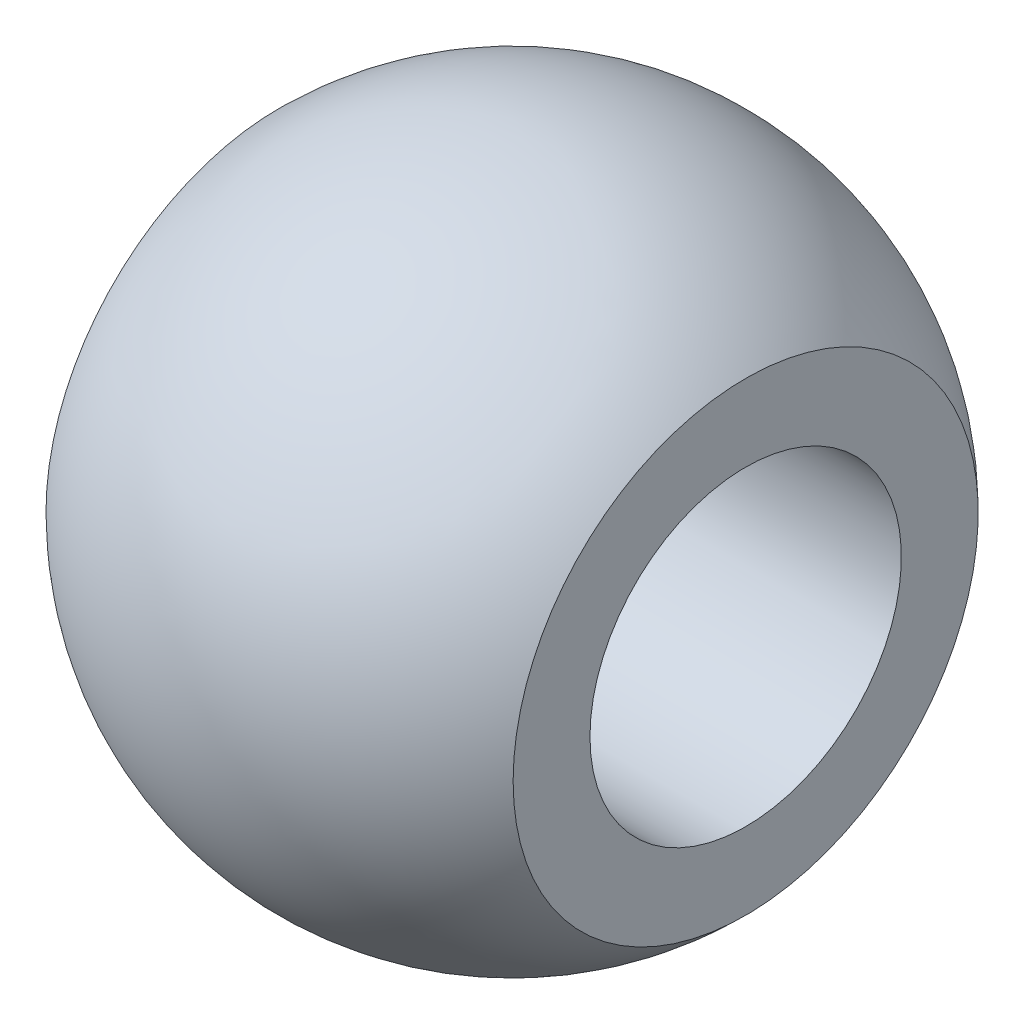
SolidWorks part; units mm, degrees
material "AISI 304"
ref_plane "前视基准面" through (0, 0, 0) normal (0, 0, 1) x (1, 0, 0)
ref_plane "上视基准面" through (0, 0, 0) normal (0, 1, 0) x (1, 0, 0)
ref_plane "右视基准面" through (0, 0, 0) normal (1, 0, 0) x (0, 0, -1)
sketch "草图1" plane through (0, 0, 0) normal (0, 0, 1) x (1, 0, 0)
  line L0 (-4.5, 3) -> (4.5, 3)
  line L1 (-13.7198, 0) -> (13.7198, 0) construction
  line L2 (0, 6.35) -> (0, 0) construction
  line L3 (4.5, 4.4802) -> (4.5, 3)
  line L4 (-4.5, 4.4802) -> (-4.5, 3)
  arc A0 (4.5, 4.4802) -> (-4.5, 4.4802) centre (0, 0) ccw
  dimension "D1" = 6
  dimension "D2" = 6.35
  dimension "D3" = 9
revolve "旋转1" add sketch "草图1" angle 360 about L1
